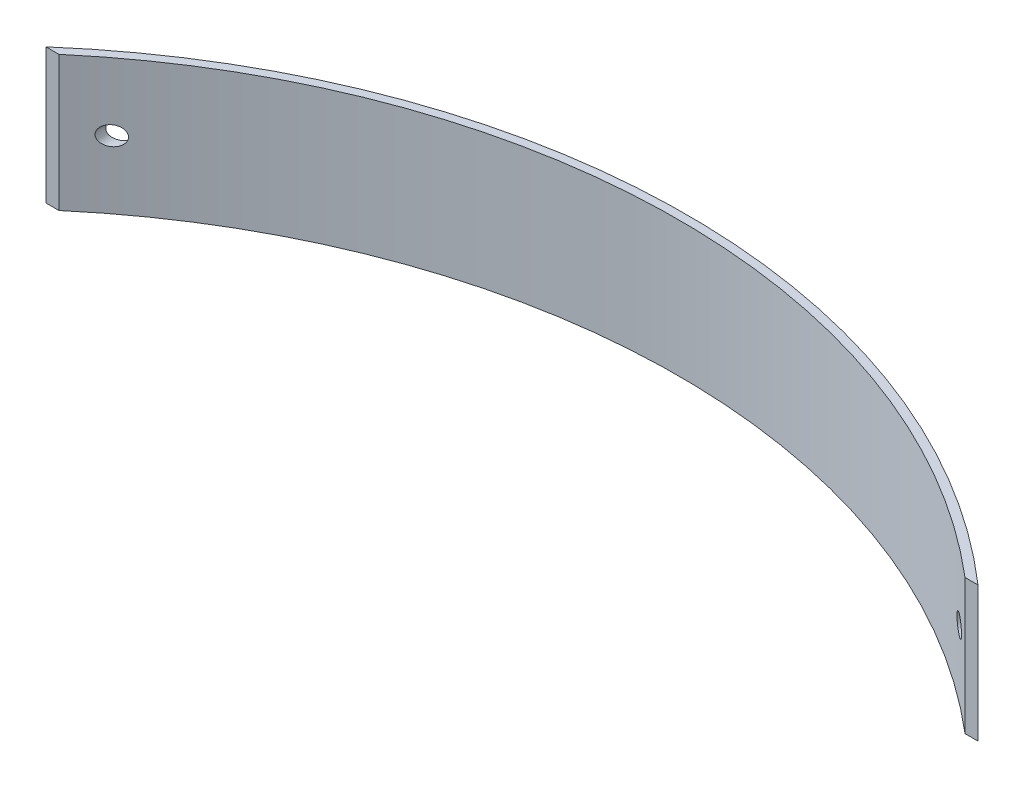
SolidWorks part; units mm, degrees
ref_plane "Front Plane" through (0, 0, 0) normal (0, 0, 1) x (1, 0, 0)
ref_plane "Top Plane" through (0, 0, 0) normal (0, 1, 0) x (1, 0, 0)
ref_plane "Right Plane" through (0, 0, 0) normal (1, 0, 0) x (0, 0, -1)
sketch "Sketch1" plane through (0, 0, 0) normal (0, 1, 0) x (1, 0, 0)
  line L0 (170.1396, 0) -> (175, 0)
  line L16 (-175, 0) -> (-170.1396, 0)
  line L20 (-170.1396, 0) -> (170.1396, 0) construction
  arc A2 (175, 0) -> (-175, 0) centre (0, -200.0147) ccw
  arc A3 (170.1396, 0) -> (-170.1396, 0) centre (0, -200.0147) ccw
  point P0 (0, 65.75)
  point P2 (0, 0)
  point P5 (0, 0)
  point P6 (0, 0)
  point P7 (0, 0)
  dimension "D2" = 3.175
  dimension "D3" = 65.75
  dimension "D1" = 350
extrude "Curved Plate" add sketch "Sketch1" along normal blind 50.8
sketch "Sketch3" plane through (0, 0, 0) normal (0, 0, 1) x (1, 0, 0)
  line L2 (-175, 0) -> (-170.1396, 0) construction
  circle A0 centre (-159.125, 25.4) radius 3.5687
  circle A1 centre (159.125, 25.4) radius 3.5687
  dimension "D1" = 7.1374
  dimension "D4" = 25.4
  dimension "D2" = 15.875
  dimension "D3" = 15.875
extrude "Mounting Holes" cut sketch "Sketch3" against normal through all
